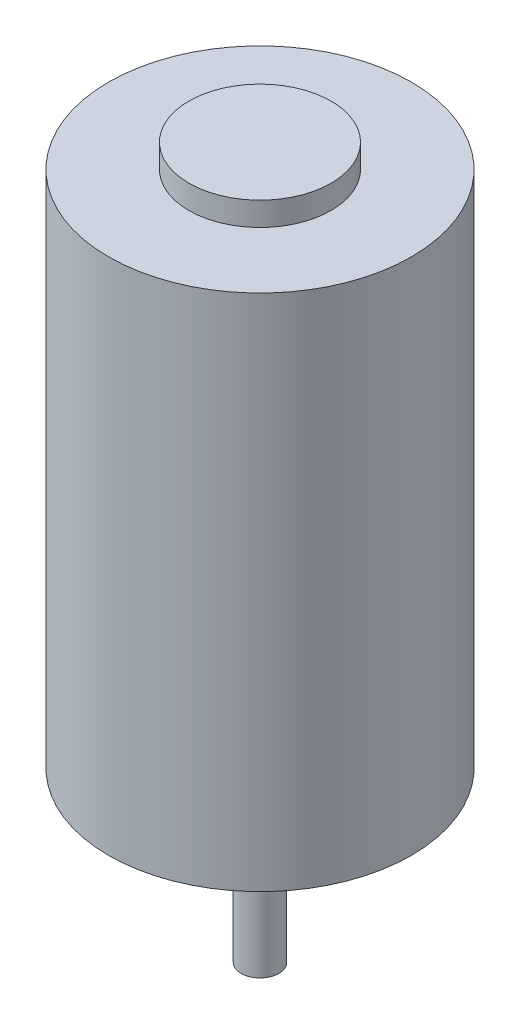
SolidWorks part; units mm, degrees
ref_plane "Front Plane" through (0, 0, 0) normal (0, 0, 1) x (1, 0, 0)
ref_plane "Top Plane" through (0, 0, 0) normal (0, 1, 0) x (1, 0, 0)
ref_plane "Right Plane" through (0, 0, 0) normal (1, 0, 0) x (0, 0, -1)
sketch "Sketch1" plane through (0, 0, 0) normal (0, 1, 0) x (1, 0, 0)
  circle A0 centre (0, 0) radius 32.004
  dimension "D1" = 64.008
extrude "Boss-Extrude1" add sketch "Sketch1" along normal blind 114.6048
sketch "Sketch2" plane through (0, 114.6048, 0) normal (0, 1, 0) x (1, 0, 0)
  circle A0 centre (0, 0) radius 15.0368
  circle A1 centre (0, 0) radius 32.004
  dimension "D1" = 30.0736
extrude "Cut-Extrude1" cut sketch "Sketch2" against normal blind 5.0038
sketch "Sketch3" plane through (0, 0, 0) normal (0, -1, 0) x (-1, 0, 0)
  line L0 (32.004, 0) -> (-32.004, 0) construction
  circle A0 centre (0, 0) radius 25.4 construction
  circle A1 centre (0, -25.4) radius 2.0193
  circle A2 centre (0, 0) radius 32.004 construction
  circle A3 centre (0, 25.4) radius 2.0193
  dimension "D1" = 50.8
  dimension "D2" = 4.0386
extrude "Cut-Extrude2" cut sketch "Sketch3" against normal blind 13.6144
sketch "Sketch4" plane through (0, 0, 0) normal (0, -1, 0) x (1, 0, 0)
  circle A0 centre (0, 0) radius 9.525
  dimension "D1" = 19.05
extrude "Boss-Extrude2" add sketch "Sketch4" along normal blind 3.9878
sketch "Sketch6" plane through (0, 0, 0) normal (0, -1, 0) x (-1, 0, 0)
  circle A0 centre (0, 0) radius 4.0005
  dimension "D1" = 8.001
extrude "Boss-Extrude3" add sketch "Sketch6" along normal blind 35.6108
